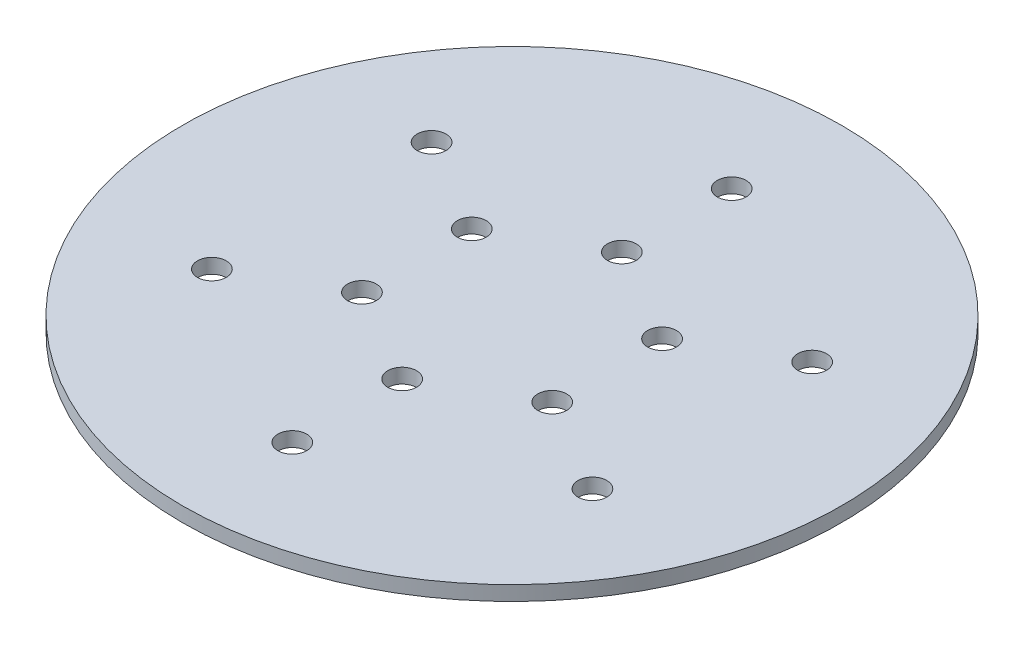
SolidWorks part; units mm, degrees
ref_plane "Front Plane" through (0, 0, 0) normal (0, 0, 1) x (1, 0, 0)
ref_plane "Top Plane" through (0, 0, 0) normal (0, 1, 0) x (1, 0, 0)
ref_plane "Right Plane" through (0, 0, 0) normal (1, 0, 0) x (0, 0, -1)
sketch "Sketch2" plane through (0, 0, 0) normal (0, 1, 0) x (1, 0, 0)
  line L0 (0, 0) -> (0, 76.2) construction
  circle A0 centre (0, 0) radius 114.3
  circle A1 centre (0, 38.1) radius 5
  circle A2 centre (0, 76.2) radius 5
  circle A3 centre (65.9911, 38.1) radius 5
  circle A4 centre (32.9956, 19.05) radius 5
  circle A5 centre (65.9911, -38.1) radius 5
  circle A6 centre (32.9956, -19.05) radius 5
  circle A7 centre (0, -76.2) radius 5
  circle A8 centre (0, -38.1) radius 5
  circle A9 centre (-65.9911, -38.1) radius 5
  circle A10 centre (-32.9956, -19.05) radius 5
  circle A11 centre (-65.9911, 38.1) radius 5
  circle A12 centre (-32.9956, 19.05) radius 5
  point P29 (0, 0)
  dimension "D1" = 228.6
  dimension "D3" = 6
  dimension "D4" = 10
  dimension "D2" = 76.2
extrude "Boss-Extrude1" add sketch "Sketch2" along normal blind 5.08
